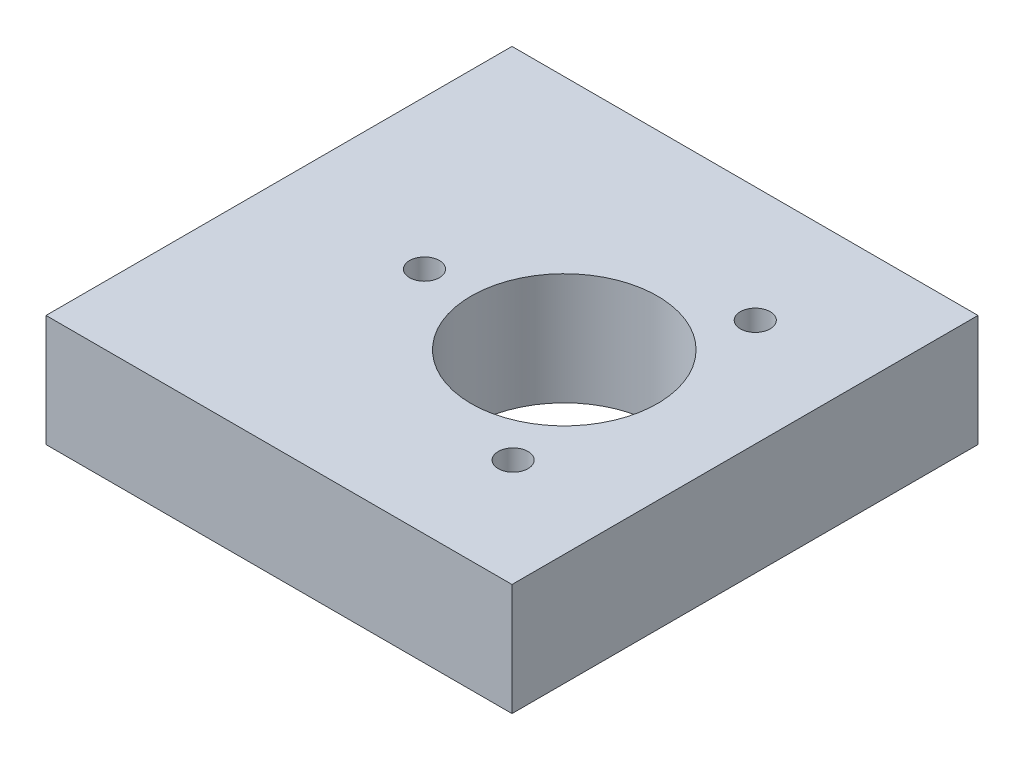
SolidWorks part; units mm, degrees
ref_plane "前视基准面" through (0, 0, 0) normal (0, 0, 1) x (1, 0, 0)
ref_plane "上视基准面" through (0, 0, 0) normal (0, 1, 0) x (1, 0, 0)
ref_plane "右视基准面" through (0, 0, 0) normal (1, 0, 0) x (0, 0, -1)
sketch "草图1" plane through (0, 0, 0) normal (0, 0, 1) x (1, 0, 0)
  line L1 (-26.4741, -1.9257) -> (23.5259, -1.9257)
  line L2 (-26.4741, -1.9257) -> (-26.4741, -13.9257)
  line L3 (-26.4741, -13.9257) -> (23.5259, -13.9257)
  line L4 (23.5259, -1.9257) -> (23.5259, -13.9257)
extrude "凸台-拉伸1" add sketch "草图1" along normal blind 50
sketch "草图2" plane through (0, 0, 0) normal (0, 0, -1) x (-1, 0, 0)
  line L0 (-23.5259, -7.9257) -> (14.4741, -7.9257)
  line L1 (-23.5259, -13.9257) -> (-23.5259, -1.9257) construction
hole_wizard "M4 螺纹孔1" positions "草图3" profile "草图4" tap size "M4" standard "GB"
sketch "草图3" plane through (0, 0, 0) normal (0, 0, -1) x (-1, 0, 0)
  line L0 (-23.5259, -7.9257) -> (14.4741, -7.9257) construction
  point P0 (-4.5259, -7.9257)
  point P4 (14.4741, -7.9257)
sketch "草图4" plane through (4.5259, -7.9257, 0) normal (1, 0, 0) x (0, 1, 0)
  line L0 (0, 0) -> (0, 11.0914)
  line L1 (0, 11.0914) -> (1.65, 10.1)
  line L2 (1.65, 10.1) -> (1.65, 0)
  line L5 (1.65, 0) -> (0, 0)
  line L10 (0, 11.0914) -> (-1.65, 10.1) construction
  line L11 (0, -6.35) -> (0, 107.95) construction
  dimension "螺纹孔钻头直径" = 3.3
  dimension "螺纹孔钻头深度" = 10.1
  dimension "导头角度" = 118
cosmetic thread "孔螺蚊线1" parameters "D1"=8, "D2"=4
cosmetic thread "孔螺蚊线2" parameters "D1"=8, "D2"=4
sketch "草图5" plane through (0, -1.9257, 0) normal (0, 1, 0) x (1, 0, 0)
  line L0 (4.5259, 0) -> (4.5259, -25.3894)
  line L1 (23.5259, 0) -> (-14.4741, 0) construction
  line L2 (4.5259, -25.3894) -> (-10.4741, -25.3894)
  line L3 (4.5259, -25.3894) -> (15.2242, -6.8594)
  line L4 (4.5259, -25.3894) -> (15.4938, -44.3864)
  circle A0 centre (4.5259, -25.3894) radius 10
  circle A1 centre (4.5259, -25.3894) radius 15
  circle A2 centre (12.0259, -12.3991) radius 1.6
  circle A3 centre (12.0259, -38.3798) radius 1.6
  circle A4 centre (-10.4741, -25.3894) radius 1.6
extrude "切除-拉伸1" cut sketch "草图5" against normal blind 50 contours L2 A0 L4 | L0 A0 L2 | L4 A0 L3 | L3 A0 L0 | L3 A2 A1 | A1 A2 L3 | L3 A2 A1 | A1 A2 L3 | A1 A3 L4 | L4 A3 A1 | A1 A3 L4 | L4 A3 A1 | A1 A4 | A1 A4 L2 | L2 A4 A1
